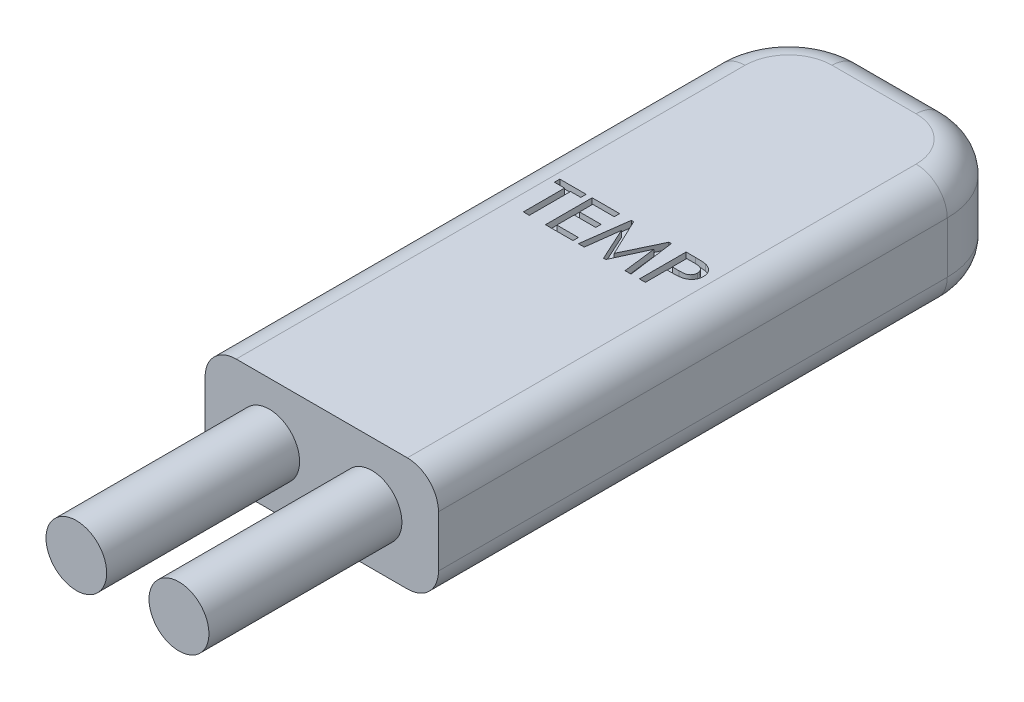
SolidWorks part; units mm, degrees
material "1060-H12"
ref_plane "Front Plane" through (0, 0, 0) normal (0, 0, 1) x (1, 0, 0)
ref_plane "Top Plane" through (0, 0, 0) normal (0, 1, 0) x (1, 0, 0)
ref_plane "Right Plane" through (0, 0, 0) normal (1, 0, 0) x (0, 0, -1)
sketch "Sketch1" plane through (0, 0, 0) normal (0, 1, 0) x (1, 0, 0)
  line L1 (-13.1623, 0) -> (-20.6623, 0)
  line L2 (-13.1623, 0) -> (-13.1623, 18.75)
  line L3 (-13.1623, 18.75) -> (-20.6623, 18.75)
  line L4 (-20.6623, 0) -> (-20.6623, 18.75)
  dimension "D1" = 7.5
  dimension "D2" = 18.75
extrude "Boss-Extrude1" add sketch "Sketch1" along normal blind 3.65
fillet "Fillet1" radius 2.4 2 edges at (-20.6623, 1.825, -18.75) (-13.1623, 1.825, -18.75)
fillet "Fillet2" radius 1 10 edges at (-20.6623, 0, -8.175) (-19.9593, 0, -18.0471) (-16.9123, 0, -18.75) (-13.8652, 0, -18.0471) (-20.6623, 3.65, -8.175) (-19.9593, 3.65, -18.0471) (-16.9123, 3.65, -18.75) (-13.8652, 3.65, -18.0471) (-13.1623, 0, -8.175) (-13.1623, 3.65, -8.175)
sketch "Sketch2" plane through (0, 3.65, 0) normal (0, 1, 0) x (1, 0, 0)
  text T0 "<b>TEMP</b>" font "Century Gothic" height 1.5
extrude "Cut-Extrude1" cut sketch "Sketch2" against normal blind 0.2
sketch "Sketch3" plane through (0, 0, 0) normal (0, 0, 1) x (1, 0, 0)
  circle A0 centre (-18.5995, 1.8124) radius 0.9748
  circle A1 centre (-15.3012, 1.7661) radius 0.9625
  point P4 (-15.3012, 1.7661)
extrude "Boss-Extrude2" add sketch "Sketch3" along normal blind 6.2
